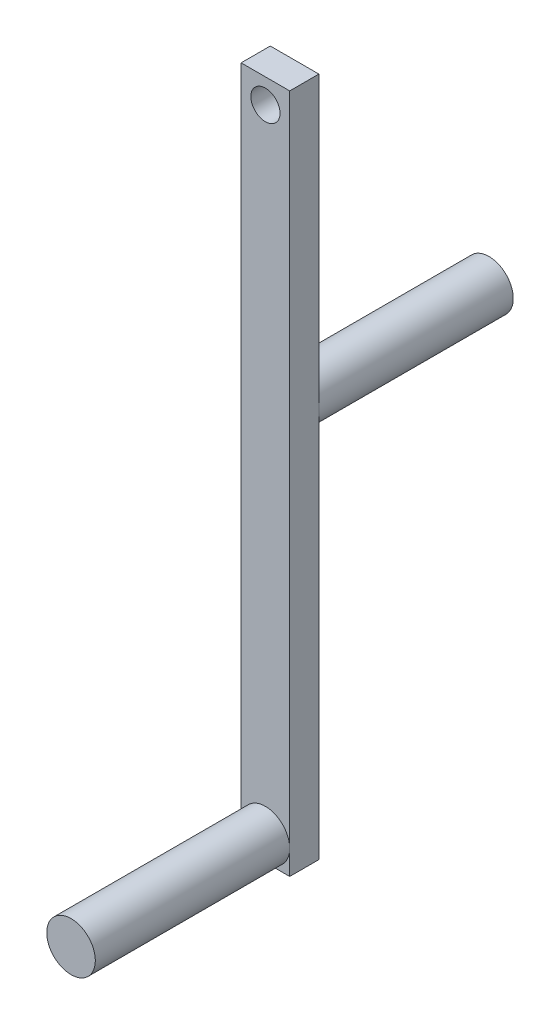
SolidWorks part; units mm, degrees
ref_plane "Front Plane" through (0, 0, 0) normal (0, 0, 1) x (1, 0, 0)
ref_plane "Top Plane" through (0, 0, 0) normal (0, 1, 0) x (1, 0, 0)
ref_plane "Right Plane" through (0, 0, 0) normal (1, 0, 0) x (0, 0, -1)
sketch "Sketch1" plane through (0, 0, 0) normal (0, 0, 1) x (1, 0, 0)
  line L1 (0, 0) -> (5, 0)
  line L2 (0, 0) -> (0, 70)
  line L3 (0, 70) -> (5, 70)
  line L4 (5, 0) -> (5, 70)
  dimension "D1" = 70
  dimension "D2" = 5
extrude "Boss-Extrude1" add sketch "Sketch1" along normal blind 3
sketch "Sketch2" plane through (0, 0, 3) normal (0, 0, 1) x (1, 0, 0)
  line L0 (5, 0) -> (5, 70) construction
  line L1 (0, 70) -> (0, 0) construction
  line L2 (0, 0) -> (5, 0) construction
  circle A0 centre (2.5, 2.5) radius 2.5
extrude "Boss-Extrude2" add sketch "Sketch2" along normal blind 20
sketch "Sketch3" plane through (0, 0, 0) normal (0, 0, -1) x (-1, 0, 0)
  line L0 (0, 0) -> (-5, 0) construction
  line L1 (-5, 0) -> (-5, 70) construction
  line L2 (0, 70) -> (0, 0) construction
  circle A0 centre (-2.5, 40) radius 2.5
  dimension "D1" = 40
extrude "Boss-Extrude3" add sketch "Sketch3" along normal blind 20
sketch "Sketch4" plane through (0, 0, 0) normal (0, 0, -1) x (-1, 0, 0)
  line L1 (-5, 70) -> (0, 70) construction
  circle A0 centre (-2.5, 67.5) radius 1.5
  point P2 (0, 0)
  point P5 (-2.5, 70)
  dimension "D1" = 3
  dimension "D2" = 2.5
extrude "Cut-Extrude1" cut sketch "Sketch4" against normal blind 20
